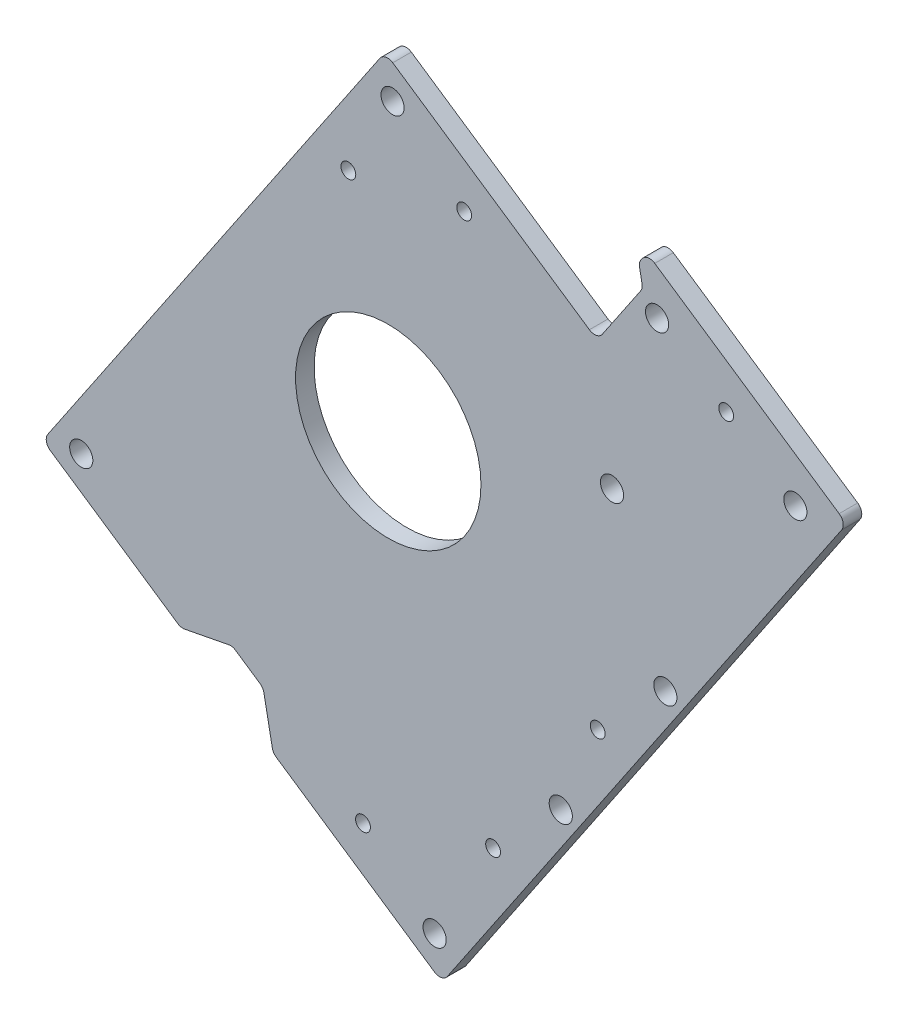
SolidWorks part; units mm, degrees
ref_plane "Front Plane" through (0, 0, 0) normal (0, 0, 1) x (1, 0, 0)
ref_plane "Top Plane" through (0, 0, 0) normal (0, 1, 0) x (1, 0, 0)
ref_plane "Right Plane" through (0, 0, 0) normal (1, 0, 0) x (0, 0, -1)
sketch "Sketch1" plane through (0, 0, 0) normal (0, 0, 1) x (1, 0, 0)
  line L0 (0, 31.75) -> (0, 57.15) construction
  line L1 (31.75, 0) -> (67.31, 0) construction
  line L3 (0, -31.75) -> (0, -97.79) construction
  line L4 (22.4506, -22.4506) -> (58.3717, -58.3717) construction
  line L5 (-22.4506, -22.4506) -> (-72.7401, -72.7401) construction
  line L6 (57.493, 23.8144) -> (29.3332, 12.1502) construction
  line L7 (-40.4112, 40.4112) -> (-22.4506, 22.4506) construction
  line L8 (42.2072, 42.2072) -> (22.4506, 22.4506) construction
  line L9 (71.5729, -29.6465) -> (29.3332, -12.1502) construction
  line L10 (33.5345, -80.9596) -> (12.1502, -29.3332) construction
  line L11 (-37.4226, -90.3462) -> (-12.1502, -29.3332) construction
  circle A0 centre (0, 0) radius 31.75 construction
  circle A3 centre (0, 0) radius 50.8 construction
  dimension "D4" = 63.5
  dimension "D24" = 101.6
  dimension "D2" = 25.4
  dimension "D3" = 35.56
  dimension "D5" = 66.04
  dimension "D6" = 45
  dimension "D7" = 50.8
  dimension "D8" = 71.12
  dimension "D9" = 45
  dimension "D10" = 45
  dimension "D11" = 27.94
  dimension "D12" = 45
  dimension "D13" = 22.5
  dimension "D14" = 22.5
  dimension "D15" = 22.5
  dimension "D16" = 25.4
  dimension "D17" = 45.72
  dimension "D18" = 55.88
  dimension "D19" = 66.04
  dimension "D20" = 22.5
  dimension "D21" = 30.48
sketch "Sketch6" plane through (0, 0, 0) normal (0, 0, 1) x (1, 0, 0)
  line L0 (0, 0) -> (0, 57.15) construction
  line L1 (-68.0069, -76.6709) -> (-109.4868, -48.6565)
  line L2 (-109.4868, -48.6565) -> (-73.9468, 3.9663) construction
  line L3 (-73.9468, 3.9663) -> (-56.6244, -7.7327)
  line L4 (-73.9468, 3.9663) -> (-1.0899, 111.8431)
  line L5 (-1.0899, 111.8431) -> (135.7295, 19.4391)
  line L6 (135.7295, 19.4391) -> (18.4476, -154.2162)
  line L7 (18.4476, -154.2162) -> (-118.3718, -61.8122)
  line L8 (-118.3718, -61.8122) -> (-109.4868, -48.6565)
  arc A0 (0, 57.15) -> (-56.6244, -7.7327) centre (0, 0) ccw
  arc A1 (0, 57.15) -> (70.8293, -29.3385) centre (1.3636, -13.9802) cw
  spline S0 degree 4 poles (72.5802, -14.4204) (72.5732, -14.8939) (72.5509, -15.8408) (72.5026, -17.0238) (72.4142, -18.4418) (72.3202, -19.622) (72.2329, -20.5651) (72.1094, -21.7358) (71.9666, -22.9009) (71.8046, -24.0602) (71.6239, -25.2132) (71.4679, -26.1331) (71.3203, -26.9417) (71.191, -27.6137) (71.0723, -28.2005) (70.9682, -28.6984) (70.8717, -29.1472) (70.8012, -29.4669) (70.7133, -29.8548) (70.619, -30.2629) (70.5011, -30.7621) (70.364, -31.3222) (70.1993, -31.971) (70.0005, -32.7239) (69.7951, -33.4698) (69.582, -34.2143) (69.3614, -34.9567) (69.1333, -35.6968) (68.8388, -36.6189) (68.4706, -37.7207) (68.0195, -38.9988) (67.4748, -40.4488) (66.9013, -41.8877) (66.2993, -43.3149) (65.6691, -44.7298) (65.0111, -46.132) (64.3256, -47.521) (63.613, -48.8963) (62.8736, -50.2574) (62.1078, -51.6038) (61.3159, -52.935) (60.4985, -54.2507) (59.6557, -55.5503) (58.5712, -57.1543) (57.221, -59.0453) (55.576, -61.2004) (53.604, -63.5903) (51.5433, -65.9041) (49.3973, -68.139) (47.1695, -70.2924) (44.8635, -72.3618) (42.4828, -74.3448) (40.0312, -76.2394) (36.8825, -78.4946) (32.9768, -81.016) (28.2508, -83.6809) (21.4155, -86.9191) (14.3083, -89.5267) (6.997, -91.4882) (-0.4519, -92.7974) (-6.6169, -93.4564) (-12.812, -93.702) (-19.0096, -93.5373) (-25.1831, -92.9667) (-31.3064, -91.9964) (-36.5985, -90.8043) (-41.0725, -89.5432) (-44.7523, -88.3359) (-47.6642, -87.2776) (-50.5413, -86.1284) (-53.3811, -84.8896) (-56.1809, -83.563) (-58.5935, -82.3267) (-60.6334, -81.2142) (-62.3138, -80.2525) (-63.6461, -79.4625) (-64.9661, -78.6522) (-66.2736, -77.8217) (-67.4063, -77.0777) (-68.3692, -76.4276) (-69.1659, -75.8779) (-69.7996, -75.4335) (-70.4313, -74.9832) (-71.06, -74.5278) (-71.6725, -74.0775) (-72.2987, -73.6093) (-72.9683, -73.0996) (-73.347, -72.808) (-73.9663, -72.325) (-74.6801, -71.7609) (-75.4046, -71.175) (-76.2838, -70.4507) (-77.1319, -69.735) (-77.9818, -69.0025) (-78.8195, -68.2643) (-79.6511, -67.5155) (-80.4737, -66.7585) (-81.4921, -65.8008) (-82.6974, -64.6343) (-83.8818, -63.4463) (-85.0447, -62.2374) (-85.8084, -61.4205) (-86.1873, -61.0093) (-86.376, -60.8031) knots 0 0 0 0 0 0.008941 0.017882 0.022352 0.026823 0.031293 0.035764 0.044578 0.048985 0.053392 0.057799 0.062207 0.06441 0.066614 0.068817 0.071021 0.072848 0.074676 0.076504 0.078332 0.081987 0.085642 0.089298 0.092953 0.096609 0.100264 0.103919 0.107575 0.114886 0.122197 0.129507 0.136818 0.144129 0.15144 0.158751 0.166062 0.173372 0.180683 0.187994 0.195305 0.202616 0.209927 0.217237 0.231859 0.246481 0.261102 0.275724 0.290346 0.304967 0.319589 0.334211 0.348832 0.363454 0.392697 0.421941 0.451184 0.506141 0.535384 0.564627 0.593871 0.623114 0.652357 0.681601 0.710844 0.740087 0.754709 0.769331 0.783952 0.798574 0.813196 0.827817 0.842439 0.84975 0.857061 0.864371 0.871682 0.878993 0.886304 0.889959 0.893615 0.89727 0.900926 0.904581 0.908237 0.911892 0.915547 0.918186 0.920826 0.926104 0.931382 0.936661 0.941939 0.947217 0.952495 0.957774 0.963052 0.96833 0.978887 0.989443 0.994722 1 1 1 1 1 construction
  spline S1 degree 4 poles (70.8293, -29.3385) (70.8117, -29.4183) (70.776, -29.5781) (70.7133, -29.8548) (70.619, -30.2629) (70.5011, -30.7621) (70.364, -31.3222) (70.1993, -31.971) (70.0005, -32.7239) (69.7951, -33.4698) (69.582, -34.2143) (69.3614, -34.9567) (69.1333, -35.6968) (68.8388, -36.6189) (68.4706, -37.7207) (68.0195, -38.9988) (67.4748, -40.4488) (66.9013, -41.8877) (66.2993, -43.3149) (65.6691, -44.7298) (65.0111, -46.132) (64.3256, -47.521) (63.613, -48.8963) (62.8736, -50.2574) (62.1078, -51.6038) (61.3159, -52.935) (60.4985, -54.2507) (59.6557, -55.5503) (58.5712, -57.1543) (57.221, -59.0453) (55.576, -61.2004) (53.604, -63.5903) (51.5433, -65.9041) (49.3973, -68.139) (47.1695, -70.2924) (44.8635, -72.3618) (42.4828, -74.3448) (40.0312, -76.2394) (36.8825, -78.4946) (32.9768, -81.016) (28.2508, -83.6809) (21.4155, -86.9191) (14.3083, -89.5267) (6.997, -91.4882) (-0.4519, -92.7974) (-6.6169, -93.4564) (-12.812, -93.702) (-19.0096, -93.5373) (-25.1831, -92.9667) (-31.3064, -91.9964) (-36.5985, -90.8043) (-41.0725, -89.5432) (-44.7523, -88.3359) (-47.6642, -87.2776) (-50.5413, -86.1284) (-53.3811, -84.8896) (-56.1809, -83.563) (-58.5935, -82.3267) (-60.6334, -81.2142) (-62.3138, -80.2525) (-63.6461, -79.4625) (-64.9661, -78.6522) (-66.2224, -77.8543) (-67.143, -77.2506) (-67.7363, -76.8537) (-68.0069, -76.6709) knots 0.071021 0.071021 0.071021 0.071021 0.071021 0.072848 0.074676 0.076504 0.078332 0.081987 0.085642 0.089298 0.092953 0.096609 0.100264 0.103919 0.107575 0.114886 0.122197 0.129507 0.136818 0.144129 0.15144 0.158751 0.166062 0.173372 0.180683 0.187994 0.195305 0.202616 0.209927 0.217237 0.231859 0.246481 0.261102 0.275724 0.290346 0.304967 0.319589 0.334211 0.348832 0.363454 0.392697 0.421941 0.451184 0.506141 0.535384 0.564627 0.593871 0.623114 0.652357 0.681601 0.710844 0.740087 0.754709 0.769331 0.783952 0.798574 0.813196 0.827817 0.842439 0.84975 0.857061 0.864371 0.871682 0.878993 0.885158 0.885158 0.885158 0.885158 0.885158
  dimension "D1" = 57.15
  dimension "D2" = 101.6
  dimension "D3" = 63.5
  dimension "D4" = 63.5
  dimension "D5" = 15.875
  dimension "D6" = 101.6
  dimension "D7" = 209.55
extrude "Boss-Extrude2" add sketch "Sketch6" along normal blind 6.35
sketch "Sketch8" plane through (0, 0, 6.35) normal (0, 0, 1) x (1, 0, 0)
  line L0 (-71.0112, -93.7982) -> (-53.3787, -90.3816)
  line L1 (-118.3718, -61.8122) -> (18.4476, -154.2162) construction
  line L2 (-53.3787, -90.3816) -> (-42.8541, -97.4896)
  line L3 (-42.8541, -97.4896) -> (-39.4375, -115.1222)
  line L4 (-39.4375, -115.1222) -> (-71.0112, -93.7982)
  line L5 (18.4476, -154.2162) -> (135.7295, 19.4391) construction
  dimension "D1" = 82.55
  dimension "D2" = 12.7
  dimension "D3" = 12.7
  dimension "D4" = 45
  dimension "D5" = 45
extrude "Cut-Extrude1" cut sketch "Sketch8" against normal through all
sketch "Sketch9" plane through (0, 0, 6.35) normal (0, 0, 1) x (1, 0, 0)
  line L0 (-1.0899, 111.8431) -> (-109.4868, -48.6565)
  line L1 (-1.0899, 111.8431) -> (135.7295, 19.4391)
  line L2 (-109.4868, -48.6565) -> (27.3325, -141.0605)
  line L3 (135.7295, 19.4391) -> (27.3325, -141.0605)
  line L4 (18.4476, -154.2162) -> (135.7295, 19.4391) construction
extrude "Boss-Extrude3" add sketch "Sketch9" against normal through all
sketch "Sketch10" plane through (0, 0, 6.35) normal (0, 0, 1) x (1, 0, 0)
  line L0 (76.6361, 21.2777) -> (4.9965, -84.7966) construction
  line L2 (-39.4375, -115.1222) -> (18.4476, -154.2162) construction
  line L3 (0, 0) -> (-45.2952, -45.2145) construction
  line L4 (-45.2952, -45.2145) -> (4.9965, -84.7966) construction
  line L5 (18.4476, -154.2162) -> (135.7295, 19.4391) construction
  circle A0 centre (4.9965, -84.7966) radius 3.9688
  circle A1 centre (40.8163, -31.7595) radius 3.9687
  circle A2 centre (76.6361, 21.2777) radius 3.9687
  circle A3 centre (-45.2952, -45.2145) radius 3.9687
  dimension "D1" = 7.9375
  dimension "D2" = 50
  dimension "D3" = 50
  dimension "D4" = 128
  dimension "D5" = 64
extrude "Cut-Extrude2" cut sketch "Sketch10" against normal through all
sketch "Sketch11" plane through (0, 0, 6.35) normal (0, 0, 1) x (1, 0, 0)
  circle A0 centre (0, 0) radius 4.5
  dimension "D1" = 9
extrude "Cut-Extrude4" cut sketch "Sketch11" against normal through all contours A0
sketch "Sketch12" plane through (0, 0, 6.35) normal (0, 0, 1) x (1, 0, 0)
  line L0 (135.7295, 19.4391) -> (67.3198, 65.6411)
  line L1 (135.7295, 19.4391) -> (157.0534, 51.0128)
  line L2 (67.3198, 65.6411) -> (88.6438, 97.2148)
  line L3 (157.0534, 51.0128) -> (88.6438, 97.2148)
  line L4 (135.7295, 19.4391) -> (-1.0899, 111.8431) construction
  dimension "D1" = 82.55
  dimension "D2" = 38.1
extrude "Boss-Extrude4" add sketch "Sketch12" against normal through all
sketch "Sketch13" plane through (0, 0, 6.35) normal (0, 0, 1) x (1, 0, 0)
  line L0 (40.8163, -31.7595) -> (76.6361, 21.2777) construction
  line L1 (18.4476, -154.2162) -> (157.0534, 51.0128) construction
  line L2 (58.7262, -5.2409) -> (94.8992, -29.6711) construction
  circle A0 centre (94.8992, -29.6711) radius 3.9687
  dimension "D1" = 7.9375
  dimension "D2" = 6.35
extrude "Cut-Extrude5" cut sketch "Sketch13" against normal through all
pattern_linear "LPattern1" count 2 spacing 64 along (-0.5597, -0.8287, 0) of "Cut-Extrude5"
sketch "Sketch14" plane through (0, 0, 6.35) normal (0, 0, 1) x (1, 0, 0)
  line L0 (59.0794, -82.7083) -> (94.8992, -29.6711) construction
  line L1 (76.9893, -56.1897) -> (71.727, -52.6357) construction
  line L2 (18.4476, -154.2162) -> (157.0534, 51.0128) construction
  line L3 (115.7406, 63.5892) -> (122.8486, 74.1138) construction
  line L4 (157.0534, 51.0128) -> (88.6438, 97.2148) construction
  circle A0 centre (71.727, -52.6357) radius 2.54
  circle A1 centre (35.9072, -105.6729) radius 2.54
  circle A2 centre (115.7406, 63.5892) radius 2.54
  dimension "D1" = 5.08
  dimension "D2" = 12.7
  dimension "D4" = 12.7
  dimension "D3" = 2
extrude "Cut-Extrude6" cut sketch "Sketch14" against normal through all
sketch "Sketch15" plane through (0, 0, 6.35) normal (0, 0, 1) x (1, 0, 0)
  line L0 (-118.3718, -61.8122) -> (-71.0112, -93.7982) construction
  line L1 (-39.4375, -115.1222) -> (18.4476, -154.2162) construction
  line L2 (18.4476, -154.2162) -> (157.0534, 51.0128) construction
  line L3 (-1.0899, 111.8431) -> (-118.3718, -61.8122) construction
  line L4 (67.3198, 65.6411) -> (-1.0899, 111.8431) construction
  circle A0 centre (-105.1473, -59.2498) radius 3.9687
  circle A1 centre (15.8851, -140.9917) radius 3.9687
  circle A2 centre (59.0794, -82.7083) radius 3.9687 construction
  circle A3 centre (1.4726, 98.6186) radius 3.9687
  dimension "D1" = 9.525
  dimension "D2" = 9.525
  dimension "D3" = 9.525
  dimension "D4" = 9.525
  dimension "D5" = 9.525
  dimension "D6" = 9.525
extrude "Cut-Extrude7" cut sketch "Sketch15" against normal through all
sketch "Sketch16" plane through (0, 0, 6.35) normal (0, 0, 1) x (1, 0, 0)
  line L0 (157.0534, 51.0128) -> (88.6438, 97.2148) construction
  line L1 (88.6438, 97.2148) -> (67.3198, 65.6411) construction
  line L2 (18.4476, -154.2162) -> (157.0534, 51.0128) construction
  circle A0 centre (92.0604, 79.5822) radius 3.9687
  circle A1 centre (139.4209, 47.5962) radius 3.9687
  circle A2 centre (94.8992, -29.6711) radius 3.9687 construction
  dimension "D1" = 12.7
  dimension "D2" = 12.7
  dimension "D3" = 12.7
  dimension "D4" = 12.7
extrude "Cut-Extrude8" cut sketch "Sketch16" against normal through all
sketch "Sketch19" plane through (0, 0, 6.35) normal (0, 0, 1) x (1, 0, 0)
  line L0 (88.6438, 97.2148) -> (67.3198, 65.6411) construction
  line L1 (67.3198, 65.6411) -> (-1.0899, 111.8431) construction
  line L2 (18.4476, -154.2162) -> (-118.3718, -61.8122) construction
  line L3 (-65.6802, -85.9048) -> (35.6087, 64.0702) construction
  line L4 (-73.9468, 3.9663) -> (-1.0899, 111.8431) construction
  circle A0 centre (35.6087, 64.0702) radius 3.9687 construction
  circle A1 centre (-65.6802, -85.9048) radius 3.9687
  dimension "D1" = 7.9375
  dimension "D2" = 25.4
  dimension "D3" = 19.05
  dimension "D4" = 9.525
extrude "Cut-Extrude11" cut sketch "Sketch19" against normal through all
sketch "Sketch21" plane through (0, 0, 6.35) normal (0, 0, 1) x (1, 0, 0)
  line L0 (-73.9468, 3.9663) -> (-1.0899, 111.8431) construction
  line L1 (67.3198, 65.6411) -> (-1.0899, 111.8431) construction
  line L2 (-118.3718, -61.8122) -> (-71.0112, -93.7982) construction
  line L3 (-39.4375, -115.1222) -> (18.4476, -154.2162) construction
  line L5 (-8.6493, -120.5906) -> (115.7406, 63.5892) construction
  line L6 (18.4476, -154.2162) -> (157.0534, 51.0128) construction
  line L7 (-118.3718, -61.8122) -> (-109.4868, -48.6565) construction
  circle A0 centre (-13.6663, 70.5302) radius 2.54
  circle A1 centre (26.007, 78.2175) radius 2.54
  circle A2 centre (-86.7294, -71.6888) radius 2.54
  circle A3 centre (-8.6493, -120.5906) radius 2.54
  circle A4 centre (35.9072, -105.6729) radius 2.54 construction
  dimension "D1" = 12.7
  dimension "D2" = 12.7
  dimension "D3" = 9.525
  dimension "D4" = 12.7
  dimension "D5" = 41.275
  dimension "D6" = 31.75
  dimension "D7" = 41.275
extrude "Cut-Extrude12" cut sketch "Sketch21" against normal through all
sketch "Sketch22" plane through (0, 0, 6.35) normal (0, 0, 1) x (1, 0, 0)
  circle A0 centre (0, 0) radius 31.75
  dimension "D1" = 63.5
extrude "Cut-Extrude13" cut sketch "Sketch22" against normal through all
sketch "Sketch23" plane through (0, 0, 6.35) normal (0, 0, 1) x (1, 0, 0)
  circle A0 centre (-65.6802, -85.9048) radius 5.8077
  circle A1 centre (-86.7294, -71.6888) radius 5.6104
extrude "Boss-Extrude5" add sketch "Sketch23" against normal through all
sketch "Sketch24" plane through (0, 0, 6.35) normal (0, 0, 1) x (1, 0, 0)
  circle A0 centre (-45.2952, -45.2145) radius 10.7613
  circle A1 centre (4.9965, -84.7966) radius 16.8817
  circle A2 centre (40.8163, -31.7595) radius 7.919
extrude "Boss-Extrude6" add sketch "Sketch24" against normal through all
sketch "Sketch25" plane through (0, 0, 6.35) normal (0, 0, 1) x (1, 0, 0)
  line L0 (85.8006, 93.0049) -> (87.1672, 85.9519)
  line L1 (88.6438, 97.2148) -> (67.3198, 65.6411) construction
  line L2 (87.1672, 85.9519) -> (71.5296, 62.7979)
  line L3 (71.5296, 62.7979) -> (67.3198, 65.6411)
  line L4 (67.3198, 65.6411) -> (85.8006, 93.0049)
  line L7 (67.3198, 65.6411) -> (-1.0899, 111.8431) construction
  dimension "D2" = 45
  dimension "D3" = 5.08
  dimension "D4" = 5.08
extrude "Cut-Extrude14" cut sketch "Sketch25" against normal through all
fillet "Fillet1" radius 3.175 12 edges at (-53.3787, -90.3816, 3.175) (-42.8541, -97.4896, 3.175) (-39.4375, -115.1222, 3.175) (-71.0112, -93.7982, 3.175) (-118.3718, -61.8122, 3.175) (18.4476, -154.2162, 3.175) (157.0534, 51.0128, 3.175) (87.1672, 85.9519, 3.175) (85.8006, 93.0049, 3.175) (88.6438, 97.2148, 3.175) (71.5296, 62.7979, 3.175) (-1.0899, 111.8431, 3.175)
